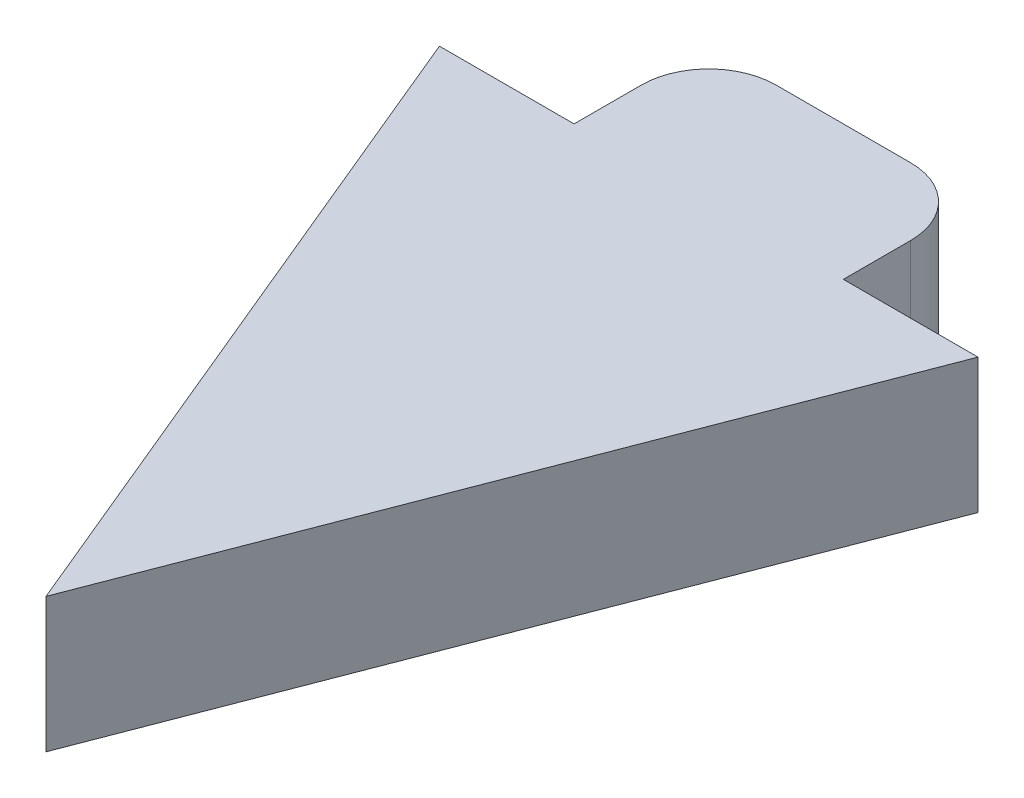
SolidWorks part; units mm, degrees
ref_plane "Front Plane" through (0, 0, 0) normal (0, 0, 1) x (1, 0, 0)
ref_plane "Top Plane" through (0, 0, 0) normal (0, 1, 0) x (1, 0, 0)
ref_plane "Right Plane" through (0, 0, 0) normal (1, 0, 0) x (0, 0, -1)
sketch "Sketch1" plane through (0, 0, 0) normal (0, 1, 0) x (1, 0, 0)
  line L0 (-5.7807, 24.019) -> (4.2193, 24.019)
  line L1 (9.2193, 19.019) -> (9.2193, 14.019)
  line L2 (-10.7807, 14.019) -> (-20.7807, 14.019)
  line L3 (-20.7807, 14.019) -> (0, -35.981)
  line L4 (-10.7807, 14.019) -> (-10.7807, 19.019)
  line L5 (0, -35.981) -> (19.2193, 14.019)
  line L6 (19.2193, 14.019) -> (9.2193, 14.019)
  arc A0 (-5.7807, 24.019) -> (-10.7807, 19.019) centre (-5.7807, 19.019) ccw
  arc A1 (4.2193, 24.019) -> (9.2193, 19.019) centre (4.2193, 19.019) cw
  point P7 (-10.7807, 24.019)
  point P10 (9.2193, 24.019)
  dimension "D5" = 5
  dimension "D1" = 20
  dimension "D2" = 10
  dimension "D3" = 10
  dimension "D4" = 10
  dimension "D6" = 10
  dimension "D7" = 50
extrude "Boss-Extrude1" add sketch "Sketch1" along normal blind 10
sketch "Sketch2" plane through (0, 0, 0) normal (0, -1, 0) x (1, 0, 0)
  line L0 (4.2193, -24.019) -> (-5.7807, -24.019) construction
  circle A0 centre (0.6356, -21.019) radius 3
  dimension "D1" = 3
extrude "Boss-Extrude2" add sketch "Sketch2" along normal blind 5
sketch "Sketch3" plane through (0, -5, 0) normal (0, -1, 0) x (1, 0, 0)
  circle A0 centre (0.6356, -21.019) radius 1.778
extrude "Cut-Extrude1" cut sketch "Sketch3" against normal blind 5
